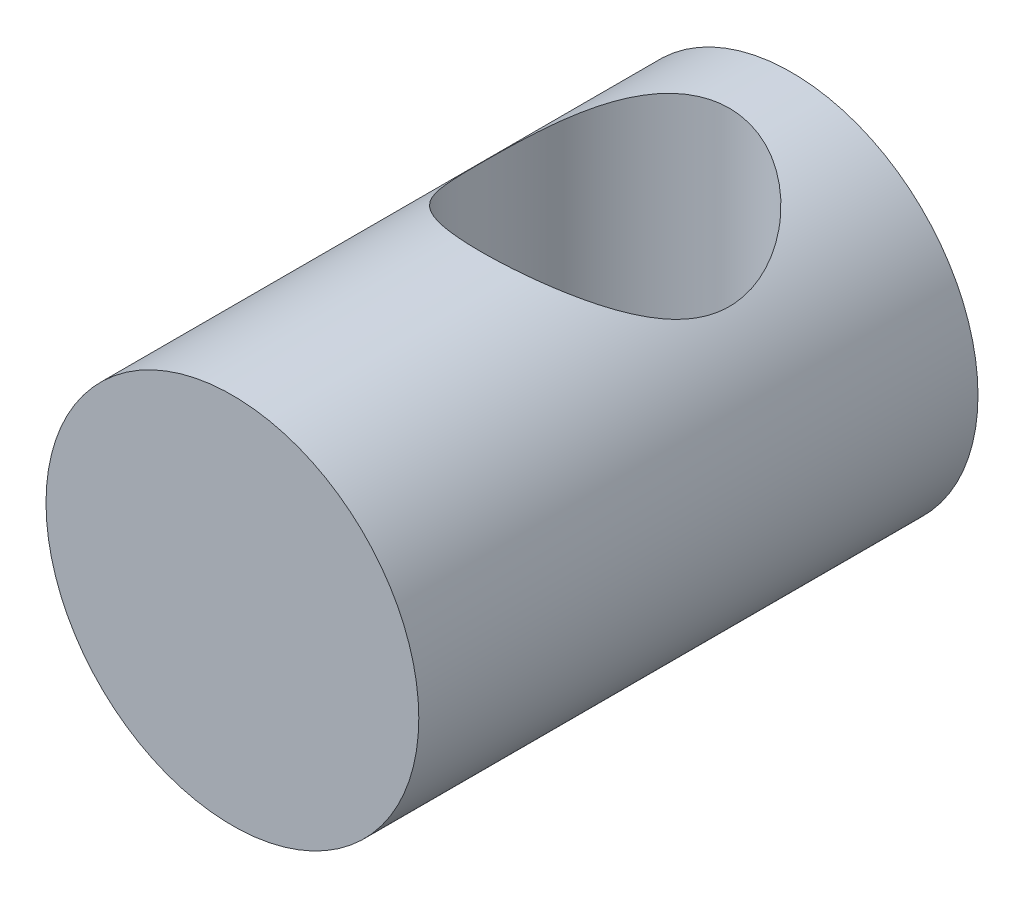
SolidWorks part; units mm, degrees
ref_plane "Front Plane" through (0, 0, 0) normal (0, 0, 1) x (1, 0, 0)
ref_plane "Top Plane" through (0, 0, 0) normal (0, 1, 0) x (1, 0, 0)
ref_plane "Right Plane" through (0, 0, 0) normal (1, 0, 0) x (0, 0, -1)
sketch "Sketch1" plane through (0, 0, 0) normal (0, 0, 1) x (1, 0, 0)
  circle A0 centre (0, 0) radius 4.7625
  dimension "D1" = 9.525
extrude "Boss-Extrude1" add sketch "Sketch1" against normal blind 14.2875
sketch "Sketch2" plane through (0, 0, 0) normal (0, 1, 0) x (1, 0, 0)
  line L0 (-4.7625, 0) -> (4.7625, 0) construction
  circle A0 centre (0, 9.525) radius 3.175
  dimension "D1" = 6.35
  dimension "D2" = 9.525
extrude "Cut-Extrude1" cut sketch "Sketch2" along normal mid plane 14.2875
